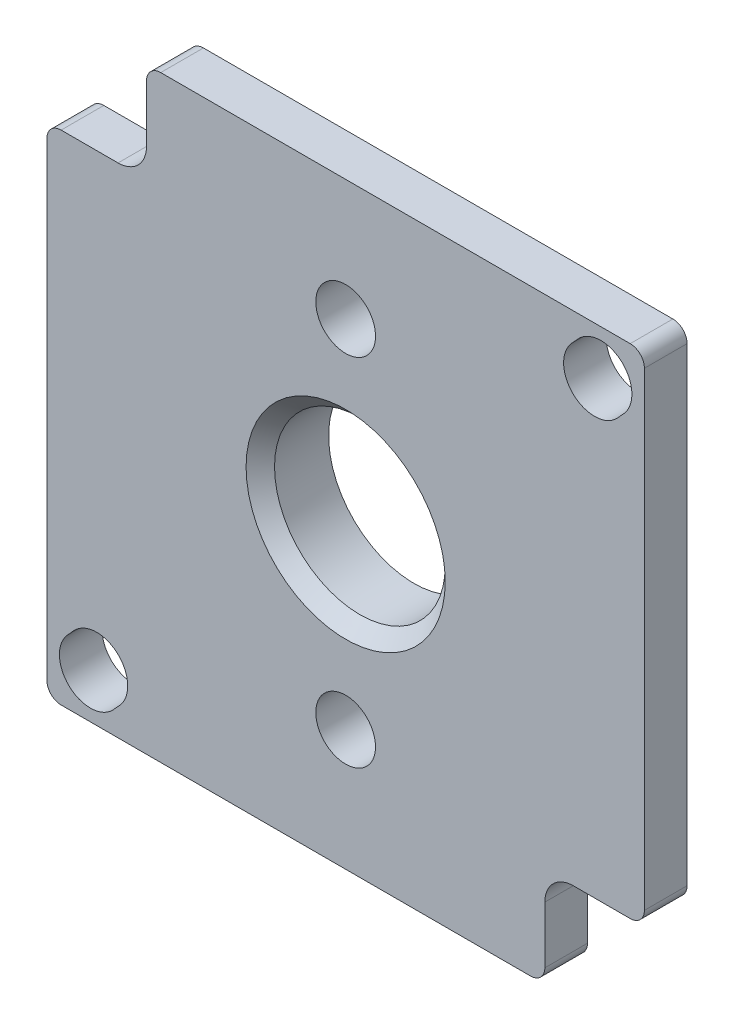
SolidWorks part; units mm, degrees
ref_plane "Front Plane" through (0, 0, 0) normal (0, 0, 1) x (1, 0, 0)
ref_plane "Top Plane" through (0, 0, 0) normal (0, 1, 0) x (1, 0, 0)
ref_plane "Right Plane" through (0, 0, 0) normal (1, 0, 0) x (0, 0, -1)
ref_plane "Plane1" through (0, 0, -1.5) normal (0, 0, -1) x (-1, 0, 0)
sketch "Sketch1" plane through (0, 0, -1.5) normal (0, 0, -1) x (-1, 0, 0)
  line L0 (21, -21) -> (21, 21)
  line L1 (21, 21) -> (-21, 21)
  line L2 (-21, 21) -> (-21, -21)
  line L3 (-21, -21) -> (21, -21)
extrude "Boss-Extrude1" add sketch "Sketch1" against normal blind 3
sketch "Sketch2" plane through (0, 0, 1.5) normal (0, 0, 1) x (1, 0, 0)
  line L0 (14, -14) -> (14, -21)
  line L1 (14, -21) -> (21, -21)
  line L2 (21, -21) -> (21, -14)
  line L3 (21, -14) -> (14, -14)
extrude "Cut-Extrude1" cut sketch "Sketch2" against normal through all
sketch "Sketch3" plane through (0, 0, 1.5) normal (0, 0, 1) x (1, 0, 0)
  line L0 (-21, 14) -> (-14, 14)
  line L1 (-14, 14) -> (-14, 21)
  line L2 (-14, 21) -> (-21, 21)
  line L3 (-21, 21) -> (-21, 14)
extrude "Cut-Extrude2" cut sketch "Sketch3" against normal through all
sketch "Sketch4" plane through (0, 0, -1.5) normal (0, 0, -1) x (-1, 0, 0)
  line L0 (-19.5481, 16.5087) -> (-19.1079, 16.0279)
  line L1 (-15.8921, 18.9721) -> (-16.3323, 19.4529)
  arc A0 (-19.1079, 16.0279) -> (-15.8921, 18.9721) centre (-17.5, 17.5) ccw
  arc A1 (-16.3323, 19.4529) -> (-19.5481, 16.5087) centre (-17.9402, 17.9808) ccw
extrude "Cut-Extrude3" cut sketch "Sketch4" against normal through all
sketch "Sketch5" plane through (0, 0, 1.5) normal (0, 0, 1) x (1, 0, 0)
  line L0 (-16.3323, -19.4529) -> (-15.8921, -18.9721)
  line L1 (-19.1079, -16.0279) -> (-19.5481, -16.5087)
  arc A0 (-19.5481, -16.5087) -> (-16.3323, -19.4529) centre (-17.9402, -17.9808) ccw
  arc A1 (-15.8921, -18.9721) -> (-19.1079, -16.0279) centre (-17.5, -17.5) ccw
extrude "Cut-Extrude4" cut sketch "Sketch5" against normal through all
sketch "Sketch6" plane through (0, 0, -1.5) normal (0, 0, -1) x (-1, 0, 0)
  arc A0 (5.0542, -14.0166) -> (3.7223, -12.9547) centre (4.715, -13.0759) cw
  arc A1 (3.7223, -12.9547) -> (-3.7223, -12.9547) centre (0, -12.5) ccw
  arc A2 (-3.7223, -12.9547) -> (-5.0542, -14.0166) centre (-4.715, -13.0759) cw
  arc A3 (-5.0542, -14.0166) -> (-5.0542, 14.0166) centre (0, 0) cw
  arc A4 (-5.0542, 14.0166) -> (-3.7223, 12.9547) centre (-4.715, 13.0759) cw
  arc A5 (-3.7223, 12.9547) -> (3.7223, 12.9547) centre (0, 12.5) ccw
  arc A6 (3.7223, 12.9547) -> (5.0542, 14.0166) centre (4.715, 13.0759) cw
  arc A7 (5.0542, 14.0166) -> (5.0542, -14.0166) centre (0, 0) cw
extrude "Boss-Extrude2" add sketch "Sketch6" along normal blind 1.8
sketch "Sketch7" plane through (0, 0, -3.3) normal (0, 0, -1) x (-1, 0, 0)
  line L0 (12.18, -5.5863) -> (7.1852, -3.5174)
  arc A0 (3.7874, -7.0467) -> (3.5791, -8.6591) centre (4.2608, -7.9275) ccw
  arc A1 (3.5791, -8.6591) -> (5.2472, -12.3299) centre (0, -12.5) cw
  arc A2 (5.2472, -12.3299) -> (12.18, -5.5863) centre (0, 0) ccw
  arc A3 (7.1852, -3.5174) -> (3.7874, -7.0467) centre (0, 0) cw
extrude "Cut-Extrude5" cut sketch "Sketch7" against normal blind 1.8
sketch "Sketch8" plane through (0, 0, -3.3) normal (0, 0, -1) x (-1, 0, 0)
  line L0 (-12.18, 5.5863) -> (-7.1852, 3.5174)
  arc A0 (-3.7874, 7.0467) -> (-3.5791, 8.6591) centre (-4.2608, 7.9275) ccw
  arc A1 (-3.5791, 8.6591) -> (-5.2472, 12.3299) centre (0, 12.5) cw
  arc A2 (-5.2472, 12.3299) -> (-12.18, 5.5863) centre (0, 0) ccw
  arc A3 (-7.1852, 3.5174) -> (-3.7874, 7.0467) centre (0, 0) cw
extrude "Cut-Extrude6" cut sketch "Sketch8" against normal blind 1.8
sketch "Sketch9" plane through (0, 0, -3.3) normal (0, 0, -1) x (-1, 0, 0)
  line L0 (-7.1852, -3.5174) -> (-12.18, -5.5863)
  arc A0 (-3.5791, -8.6591) -> (-3.7874, -7.0467) centre (-4.2608, -7.9275) ccw
  arc A1 (-3.7874, -7.0467) -> (-7.1852, -3.5174) centre (0, 0) cw
  arc A2 (-12.18, -5.5863) -> (-5.2472, -12.3299) centre (0, 0) ccw
  arc A3 (-5.2472, -12.3299) -> (-3.5791, -8.6591) centre (0, -12.5) cw
extrude "Cut-Extrude7" cut sketch "Sketch9" against normal blind 1.8
sketch "Sketch10" plane through (0, 0, -3.3) normal (0, 0, -1) x (-1, 0, 0)
  line L0 (7.1852, 3.5174) -> (12.18, 5.5863)
  arc A0 (3.5791, 8.6591) -> (3.7874, 7.0467) centre (4.2608, 7.9275) ccw
  arc A1 (3.7874, 7.0467) -> (7.1852, 3.5174) centre (0, 0) cw
  arc A2 (12.18, 5.5863) -> (5.2472, 12.3299) centre (0, 0) ccw
  arc A3 (5.2472, 12.3299) -> (3.5791, 8.6591) centre (0, 12.5) cw
extrude "Cut-Extrude8" cut sketch "Sketch10" against normal blind 1.8
sketch "Sketch11" plane through (0, 0, -3.3) normal (0, 0, -1) x (-1, 0, 0)
  line L0 (12.5627, 4.6624) -> (7.5679, 2.5935)
  line L1 (7.5679, -2.5935) -> (12.5627, -4.6624)
  arc A0 (12.5627, -4.6624) -> (12.5627, 4.6624) centre (0, 0) ccw
  arc A1 (7.5679, 2.5935) -> (7.5679, -2.5935) centre (0, 0) cw
extrude "Cut-Extrude9" cut sketch "Sketch11" against normal blind 1.8
sketch "Sketch12" plane through (0, 0, -3.3) normal (0, 0, -1) x (-1, 0, 0)
  line L0 (-12.5627, -4.6624) -> (-7.5679, -2.5935)
  line L1 (-7.5679, 2.5935) -> (-12.5627, 4.6624)
  arc A0 (-12.5627, 4.6624) -> (-12.5627, -4.6624) centre (0, 0) ccw
  arc A1 (-7.5679, -2.5935) -> (-7.5679, 2.5935) centre (0, 0) cw
extrude "Cut-Extrude10" cut sketch "Sketch12" against normal blind 1.8
hole_wizard "Ø4.2 (4.2) Diameter Hole1" positions "Sketch14" profile "Sketch13" hole size "Ø4.2" standard "ANSI Metric"
sketch "Sketch14" plane through (0, 0, -1.5) normal (0, 0, -1) x (-1, 0, 0)
  point P0 (0, -12.5)
  point P1 (0, 12.5)
sketch "Sketch13" plane through (0, -12.5, -1.5) normal (1, 0, 0) x (0, 1, 0)
  line L0 (0, 0) -> (0, 3)
  line L1 (0, 3) -> (2.1, 3)
  line L2 (2.1, 3) -> (2.1, 0)
  line L5 (2.1, 0) -> (0, 0)
  line L11 (0, -6.35) -> (0, 107.95) construction
  dimension "Thru Hole Dia." = 4.2
  dimension "Thru Hole Depth" = 3
hole_wizard "Ø12.0 (12) Diameter Hole1" positions "Sketch16" profile "Sketch15" hole size "Ø12.0" standard "ANSI Metric"
sketch "Sketch16" plane through (0, 0, 1.5) normal (0, 0, 1) x (1, 0, 0)
  point P0 (0, 0)
sketch "Sketch15" plane through (0, 0, 1.5) normal (1, 0, 0) x (0, -1, 0)
  line L0 (0, 0) -> (0, 4.8)
  line L1 (0, 4.8) -> (6, 4.8)
  line L2 (6, 4.8) -> (6, 0)
  line L5 (6, 0) -> (0, 0)
  line L11 (0, -6.35) -> (0, 107.95) construction
  dimension "Thru Hole Dia." = 12
  dimension "Thru Hole Depth" = 4.8
chamfer "Chamfer1" distance 1 angle 45 1 edges at (6, 0, 1.5)
chamfer "Chamfer2" distance 0.5 angle 45 8 edges at (14.9, 0, -3.3) (4.0915, -13.8578, -3.3) (4.0915, 13.8578, -3.3) (0, -8.75, -3.3) (0, 8.75, -3.3) (-4.0915, -13.8578, -3.3) (-4.0915, 13.8578, -3.3) (-14.9, 0, -3.3)
fillet "Fillet1" radius 1 26 edges at (5.2472, 12.3299, -2.4) (-12.18, -5.5863, -2.4) (-21, 14, 0) (7.1852, 3.5174, -2.4) (-12.18, 5.5863, -2.4) (12.18, 5.5863, -2.4) (-5.2472, 12.3299, -2.4) (7.1852, -3.5174, -2.4) (14, -21, 0) (12.18, -5.5863, -2.4) (-7.1852, 3.5174, -2.4) (-7.5679, 2.5935, -2.4) (-5.2472, -12.3299, -2.4) (-12.5627, 4.6624, -2.4) (5.2472, -12.3299, -2.4) (-12.5627, -4.6624, -2.4) (-14, 21, 0) (7.5679, -2.5935, -2.4) (-21, -21, 0) (12.5627, -4.6624, -2.4) (21, 21, 0) (21, -14, 0) (-7.1852, -3.5174, -2.4) (12.5627, 4.6624, -2.4) (7.5679, 2.5935, -2.4) (-7.5679, -2.5935, -2.4)
fillet "Fillet2" radius 2 2 edges at (14, -14, 0) (-14, 14, 0)
